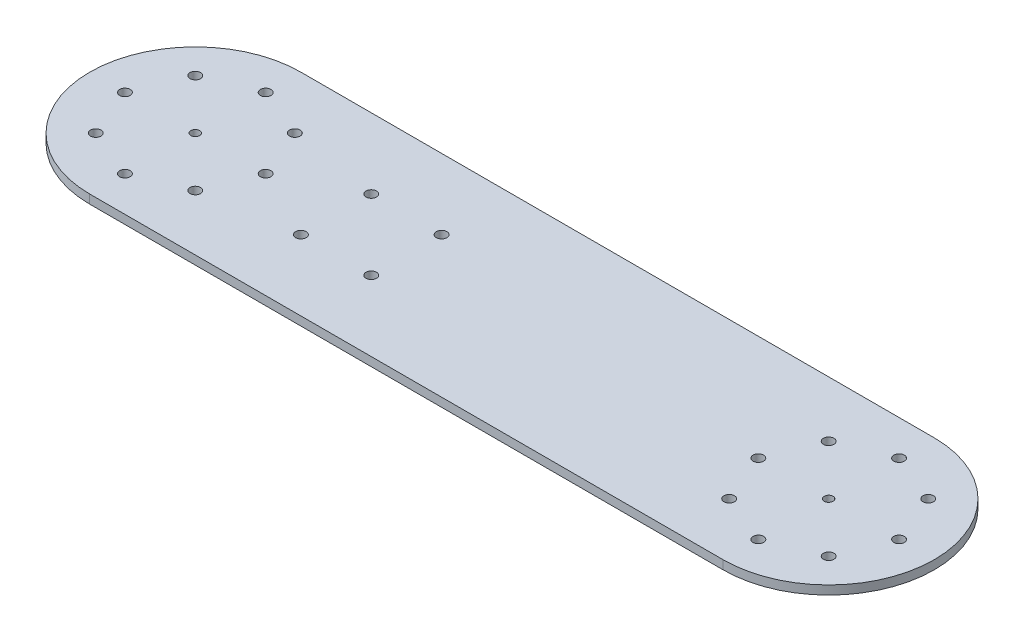
SolidWorks part; units mm, degrees
ref_plane "Front Plane" through (0, 0, 0) normal (0, 0, 1) x (1, 0, 0)
ref_plane "Top Plane" through (0, 0, 0) normal (0, 1, 0) x (1, 0, 0)
ref_plane "Right Plane" through (0, 0, 0) normal (1, 0, 0) x (0, 0, -1)
sketch "Sketch1" plane through (0, 0, 0) normal (0, 1, 0) x (1, 0, 0)
  line L0 (-228.6, 0) -> (228.6, 0) construction
  line L1 (-228.6, 50.8) -> (-228.6, -50.8) construction
  line L2 (-228.6, 76.2) -> (228.6, 76.2)
  line L4 (-228.6, -76.2) -> (228.6, -76.2)
  line L5 (-192.679, 35.921) -> (-228.6, 0) construction
  line L6 (0, 76.2) -> (0, -76.2) construction
  line L7 (-101.6, 25.4) -> (-101.6, -25.4) construction
  line L9 (-127, 25.4) -> (-76.2, 25.4) construction
  line L10 (-127, 25.4) -> (-127, -25.4) construction
  line L11 (-127, -25.4) -> (-76.2, -25.4) construction
  line L12 (-76.2, 25.4) -> (-76.2, -25.4) construction
  arc A0 (-228.6, 76.2) -> (-228.6, -76.2) centre (-228.6, 0) ccw
  arc A1 (228.6, -76.2) -> (228.6, 76.2) centre (228.6, 0) ccw
  circle A2 centre (-228.6, 0) radius 50.8 construction
  circle A4 centre (-228.6, 0) radius 3.175
  circle A6 centre (-228.6, 50.8) radius 3.81
  circle A7 centre (-192.679, 35.921) radius 3.81
  circle A8 centre (-177.8, 0) radius 3.81
  circle A9 centre (-192.679, -35.921) radius 3.81
  circle A10 centre (-228.6, -50.8) radius 3.81
  circle A11 centre (-264.521, -35.921) radius 3.81
  circle A12 centre (-279.4, 0) radius 3.81
  circle A13 centre (-264.521, 35.921) radius 3.81
  circle A14 centre (228.6, 0) radius 3.175
  circle A15 centre (279.4, 0) radius 3.81
  circle A16 centre (264.521, -35.921) radius 3.81
  circle A17 centre (228.6, -50.8) radius 3.81
  circle A18 centre (192.679, -35.921) radius 3.81
  circle A19 centre (177.8, 0) radius 3.81
  circle A20 centre (192.679, 35.921) radius 3.81
  circle A21 centre (228.6, 50.8) radius 3.81
  circle A22 centre (228.6, 0) radius 50.8 construction
  circle A23 centre (264.521, 35.921) radius 3.81
  circle A24 centre (-127, 25.4) radius 3.81
  circle A25 centre (-76.2, -25.4) radius 3.81
  circle A26 centre (-127, -25.4) radius 3.81
  circle A27 centre (-76.2, 25.4) radius 3.81
  point P28 (-228.6, 0)
  point P55 (-101.6, 25.4)
  dimension "D4" = 76.2
  dimension "D5" = 101.6
  dimension "D6" = 6.35
  dimension "D8" = 7.62
  dimension "D13" = 7.62
  dimension "D1" = 457.2
  dimension "D2" = 152.4
  dimension "D3" = 50.8
  dimension "D9" = 45
  dimension "D10" = 38.8806
  dimension "D11" = 50.8
  dimension "D12" = 127
  dimension "D7" = 8
extrude "Boss-Extrude1" add sketch "Sketch1" along normal mid plane 6.35
